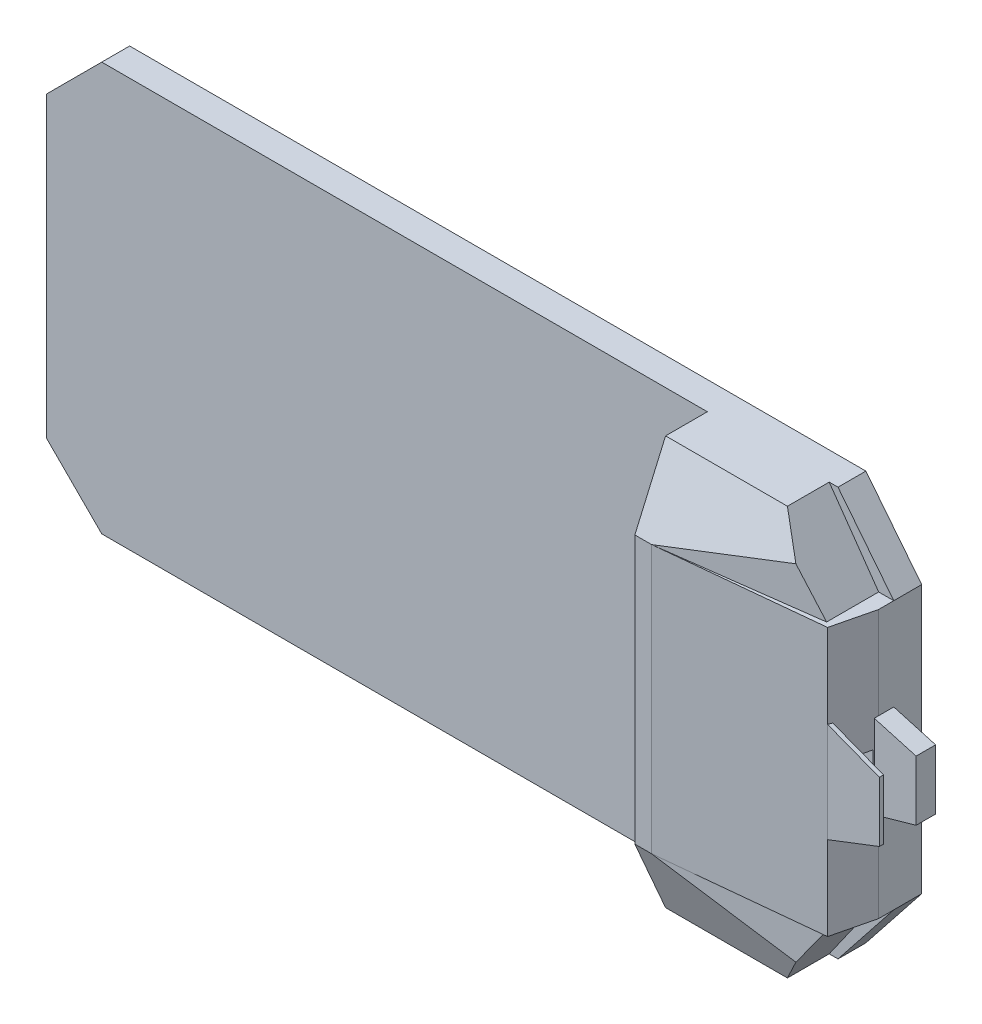
SolidWorks part; units mm, degrees
ref_plane "Alzado" through (0, 0, 0) normal (0, 0, 1) x (1, 0, 0)
ref_plane "Planta" through (0, 0, 0) normal (0, 1, 0) x (1, 0, 0)
ref_plane "Vista lateral" through (0, 0, 0) normal (1, 0, 0) x (0, 0, -1)
sketch "Sketch1" plane through (0, 0, 0) normal (0, 0, 1) x (1, 0, 0)
  line L0 (-1320, -732.5) -> (-1518.4983, -534.0017)
  line L1 (-1518.4983, -534.0017) -> (-1518.4983, 534.0017)
  line L2 (-1518.4983, 534.0017) -> (-1320, 732.5)
  line L4 (-1320, 732.5) -> (1320, 732.5)
  line L5 (1320, 732.5) -> (1520, 480)
  line L6 (1520, 480) -> (1520, -480)
  line L7 (1520, -480) -> (1320, -732.5)
  line L8 (1320, -732.5) -> (-1320, -732.5)
  line L9 (-1320, 732.5) -> (1320, -732.5) construction
  line L10 (1320, 732.5) -> (-1320, -732.5) construction
extrude "Boss-Extrude1" add sketch "Sketch1" along normal blind 100
ref_plane "Plane1" through (881.5017, 0, 0) normal (-1, 0, 0) x (0, 0, 1)
sketch "Sketch2" plane through (881.5017, 0, 0) normal (-1, 0, 0) x (0, 0, 1)
  line L0 (100, -732.5) -> (0, -732.5) construction
  line L1 (100, 732.5) -> (249.7979, 732.5)
  line L2 (100, 732.5) -> (100, -732.5)
  line L3 (100, -732.5) -> (249.7979, -732.5)
  line L5 (249.7979, -732.5) -> (360, -480)
  line L6 (360, -480) -> (360, 480)
  line L7 (360, 480) -> (249.7979, 732.5)
  point P14 (100, 0)
  point P15 (360, 0)
  dimension "D1" = 260
  dimension "D2" = 960
extrude "Boss-Extrude2" add sketch "Sketch2" along normal mid plane 60
ref_plane "Plane2" through (0, 0, 0) normal (0, 1, 0) x (1, 0, 0)
sketch "Sketch3" plane through (0, 0, 0) normal (0, 1, 0) x (1, 0, 0)
  line L0 (1520, -100) -> (1520, -154.517)
  line L1 (1520, -154.517) -> (1484.3286, -301.704)
  line L2 (1484.3286, -301.704) -> (911.5017, -360)
  line L3 (1520, -100) -> (911.5017, -100)
  line L4 (911.5017, -100) -> (911.5017, -360)
extrude "Boss-Extrude3" add sketch "Sketch3" along normal mid plane 960
ref_plane "Plane3" through (1520, 480, 154.517) normal (0, -1, 0) x (-1, 0, 0)
sketch "Sketch10" plane through (0, 0, 100) normal (0, 0, 1) x (1, 0, 0)
  line L0 (1520, 150) -> (1670, 107.5)
  line L1 (1670, 107.5) -> (1670, -107.5)
  line L3 (1670, -107.5) -> (1520, -150)
  line L4 (1520, -150) -> (1520, 150)
  line L5 (1520, 480) -> (1520, -480) construction
  point P4 (1670, 0)
  point P7 (1520, 0)
  dimension "D1" = 300
  dimension "D2" = 150
  dimension "D3" = 215
extrude "Boss-Extrude6" add sketch "Sketch10" along normal blind 70
ref_plane "Plane4" through (0, 0, 301.704) normal (0, 0, -1) x (0, -1, 0)
sketch "Sketch11" plane through (0, 0, 301.704) normal (0, 0, -1) x (0, -1, 0)
  line L0 (-178.9323, -1484.3286) -> (-107.5, -1670)
  line L1 (-480, -1484.3286) -> (480, -1484.3286) construction
  line L2 (-107.5, -1670) -> (107.5, -1670)
  line L3 (107.5, -1670) -> (159.7541, -1484.3286)
  line L4 (159.7541, -1484.3286) -> (-178.9323, -1484.3286)
extrude "Boss-Extrude7" add sketch "Sketch11" along normal blind 15
ref_plane "Plane7" through (0, 732.5, 0) normal (0, 1, 0) x (1, 0, 0)
sketch "Sketch14" plane through (0, 732.5, 0) normal (0, 1, 0) x (1, 0, 0)
  line L0 (911.5017, -100) -> (911.5017, -360)
  line L2 (911.5017, -100) -> (1376.3617, -100)
  line L3 (911.5017, -360) -> (1351.8178, -301.704)
  line L4 (1351.8178, -301.704) -> (1376.3617, -100)
  line L5 (598.914, -301.704) -> (-598.914, -301.704) construction
extrude "Boss-Extrude8" add sketch "Sketch14" against normal up to surface (252.5 mm away) up to face at (1269.4664, 480, 203.2442)
sketch "Sketch16" plane through (0, 0, 100) normal (0, 0, 1) x (1, 0, 0)
  line L0 (1329.451, 674.1238) -> (1465.7866, 480)
  line L1 (1520, 480) -> (1376.3617, 480) construction
  line L2 (1465.7866, 480) -> (1329.451, 480)
  line L4 (1329.451, 480) -> (1329.451, 674.1238)
extrude "Boss-Extrude9" add sketch "Sketch16" along normal up to surface (204.6652 mm away)
sketch "Sketch15" plane through (0, 208.7823, 478.3713) normal (0, 0.4, 0.9165) x (1, 0, 0)
  line L1 (911.5017, 834.0341) -> (1498.7216, 834.0341)
  line L2 (911.5017, 834.0341) -> (911.5017, 37.745)
  line L3 (911.5017, 37.745) -> (1498.7216, 37.745)
  line L4 (1498.7216, 834.0341) -> (1498.7216, 37.745)
  line L5 (911.5017, 834.0341) -> (1498.7216, 37.745) construction
  line L6 (911.5017, 37.745) -> (1498.7216, 834.0341) construction
  line L7 (911.5017, 295.9237) -> (911.5017, 527.3431) construction
  point P0 (1205.1116, 435.8895)
extrude "Cut-Extrude1" cut sketch "Sketch15" along normal blind 400
sketch "Sketch17" plane through (1207.3696, 847.9513, 0) normal (0.8183, 0.5747, 0) x (0, 0, -1)
  line L0 (-100, -449.6304) -> (-100, -294.0364) construction
  line L1 (-342.7525, -428.6515) -> (-100, -428.6515)
  line L2 (-342.7525, -428.6515) -> (-342.7525, 2.6529)
  line L3 (-342.7525, 2.6529) -> (-100, 2.6529)
  line L4 (-100, -428.6515) -> (-100, 2.6529)
extrude "Cut-Extrude2" cut sketch "Sketch17" along normal blind 150
sketch "Sketch18" plane through (0, 0, 0) normal (0, 1, 0) x (1, 0, 0)
  line L1 (-2084.7593, 367.4328) -> (2176.162, 367.4328)
  line L2 (-2084.7593, 367.4328) -> (-2084.7593, -1238.3439)
  line L3 (-2084.7593, -1238.3439) -> (2176.162, -1238.3439)
  line L4 (2176.162, 367.4328) -> (2176.162, -1238.3439)
extrude "Cut-Extrude3" cut sketch "Sketch18" against normal blind 1872
mirror "Mirror1" about plane through (0, 0, 0) normal (0, 1, 0) of bodies 112
sketch "Sketch19" plane through (0, 0, 170) normal (0, 0, 1) x (1, 0, 0)
  line L0 (1520, 150) -> (1520, -150) construction
  line L1 (1520, 50) -> (1480, 50)
  line L2 (1520, 50) -> (1520, -50)
  line L3 (1520, -50) -> (1480, -50)
  line L4 (1480, 50) -> (1480, -50)
  line L6 (1670, 107.5) -> (1670, -107.5) construction
  point P6 (1670, 0)
  point P7 (1480, 0)
  dimension "D1" = 40
  dimension "D2" = 100
extrude "Cut-Extrude4" cut sketch "Sketch19" along normal up to surface (116.704 mm away) up to face at (1578.982, 0, 286.704)
